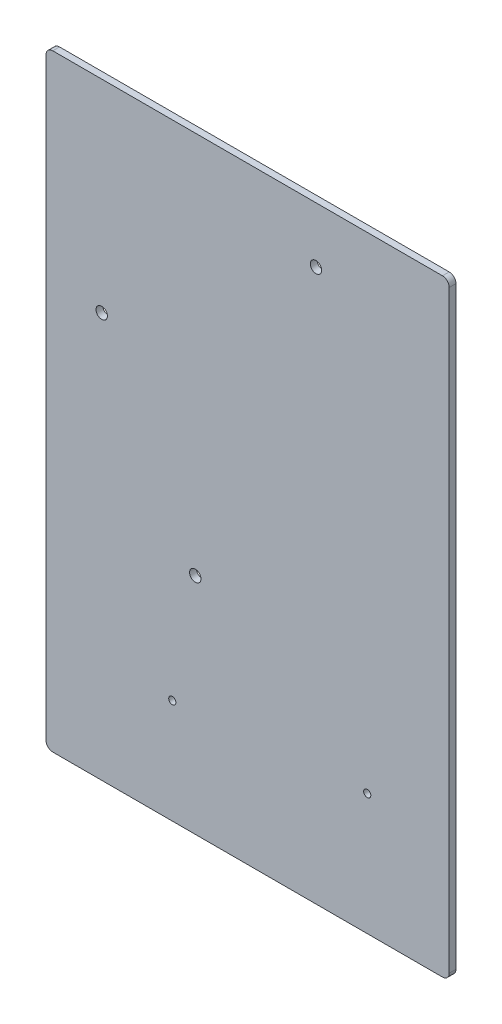
SolidWorks part; units mm, degrees
material "PC High Viscosity"
ref_plane "Front Plane" through (0, 0, 0) normal (0, 0, 1) x (1, 0, 0)
ref_plane "Top Plane" through (0, 0, 0) normal (0, 1, 0) x (1, 0, 0)
ref_plane "Right Plane" through (0, 0, 0) normal (1, 0, 0) x (0, 0, -1)
sketch "Sketch1" plane through (0, 0, 0) normal (0, 0, 1) x (1, 0, 0)
  line L0 (0, 0) -> (0, 571.5)
  line L1 (0, 0) -> (379.4125, 0)
  line L2 (381, 355.6) -> (425.45, 355.6) construction
  line L3 (381, 355.6) -> (381, 400.05) construction
  line L4 (381, 400.05) -> (425.45, 400.05) construction
  line L5 (425.45, 355.6) -> (425.45, 400.05) construction
  line L6 (379.4125, 0) -> (379.4125, 403.225)
  line L7 (379.4125, 403.225) -> (428.625, 403.225)
  line L8 (428.625, 403.225) -> (428.625, 355.6)
  line L9 (428.625, 355.6) -> (479.425, 355.6)
  line L10 (479.425, 355.6) -> (479.425, 466.725)
  line L12 (379.4125, 571.5) -> (0, 571.5)
  line L13 (379.4125, 571.5) -> (379.4125, 466.725)
  line L14 (379.4125, 466.725) -> (479.425, 466.725)
  dimension "D1" = 571.5
  dimension "D2" = 44.45
  dimension "D3" = 400.05
  dimension "D4" = 381
  dimension "D5" = 3.175
  dimension "D6" = 3.175
  dimension "D7" = 3.175
  dimension "D8" = 50.8
  dimension "D9" = 63.5
extrude "Boss-Extrude1" add sketch "Sketch1" along normal blind 6.35
fillet "Fillet1" radius 3.175 2 edges at (428.625, 403.225, 3.175) (379.4125, 403.225, 3.175)
fillet "Fillet2" radius 44.45 2 edges at (479.425, 466.725, 3.175) (379.4125, 466.725, 3.175)
hole_wizard "1/4 Clearance Hole1" positions "Sketch2" profile "Sketch3" hole size "1/4" standard "ANSI Inch" end condition through all
sketch "Sketch2" plane through (0, 0, 0) normal (0, 0, -1) x (-1, 0, 0)
  line L0 (0, 77.4886) -> (-379.4125, 110.6829) construction
  line L1 (0, 571.5) -> (0, 0) construction
  line L2 (-379.4125, 0) -> (-379.4125, 400.05) construction
  line L4 (0, 0) -> (-379.4125, 0) construction
  line L5 (-320.0116, 93.5432) -> (-104.9332, 74.7262) construction
  line L6 (-320.0116, 93.5432) -> (-316.691, 131.4982) construction
  line L7 (-104.9332, 74.7262) -> (-101.6126, 112.6813) construction
  line L8 (-316.691, 131.4982) -> (-101.6126, 112.6813) construction
  line L9 (-319.8049, 95.9065) -> (-104.7264, 77.0896) construction
  line L11 (0, 0) -> (-44.45, 0) construction
  line L12 (0, 0) -> (0, 571.5) construction
  line L13 (0, 571.5) -> (-44.45, 571.5) construction
  line L14 (-44.45, 0) -> (-44.45, 571.5) construction
  line L15 (-379.4125, 571.5) -> (0, 571.5) construction
  line L17 (-381, 0) -> (-425.45, 0) construction
  line L18 (-381, 0) -> (-381, 571.5) construction
  line L19 (-381, 571.5) -> (-425.45, 571.5) construction
  line L20 (-425.45, 0) -> (-425.45, 571.5) construction
  line L21 (-379.4125, 121.05) -> (-44.45, 91.7445) construction
  line L23 (-209.1518, 122.0897) -> (-212.4724, 84.1347) construction
  line L24 (-318.9747, 105.3953) -> (-103.8963, 86.5783) construction
  line L25 (-319.6665, 97.488) -> (-104.5881, 78.671) construction
  line L27 (-104.4497, 80.2525) -> (-319.5281, 99.0694) construction
  line L28 (-425.45, 44.45) -> (0, 44.45) construction
  point P0 (-118.8107, 98.2503)
  point P2 (-302.26, 114.3)
  point P213 (-209.1518, 122.0897)
  dimension "D2" = 5
  dimension "D3" = 2.3724
  dimension "D4" = 38.1
  dimension "D5" = 215.9
  dimension "D6" = 44.45
  dimension "D7" = 0
  dimension "D8" = 381
  dimension "D9" = 15.875
  dimension "D10" = 184.15
  dimension "D11" = 1.5875
  dimension "D12" = 1.5875
  dimension "D13" = 6.35
  dimension "D14" = 44.45
  dimension "D15" = 302.26
  dimension "D16" = 114.3
sketch "Sketch3" plane through (118.8107, 98.2503, 0) normal (1, 0, 0) x (0, 1, 0)
  line L0 (0, 0) -> (0, 6.35)
  line L1 (0, 6.35) -> (3.3782, 6.35)
  line L2 (3.3782, 6.35) -> (3.3782, 0)
  line L5 (3.3782, 0) -> (0, 0)
  line L11 (0, -6.35) -> (0, 107.95) construction
  dimension "Thru Hole Dia." = 6.7564
  dimension "Thru Hole Depth" = 6.35
sketch "Sketch4" plane through (0, 0, 0) normal (0, 0, -1) x (-1, 0, 0)
  line L1 (-379.4125, 511.175) -> (-479.425, 511.175)
  line L2 (-379.4125, 511.175) -> (-379.4125, 355.6)
  line L3 (-379.4125, 355.6) -> (-479.425, 355.6)
  line L4 (-479.425, 511.175) -> (-479.425, 355.6)
extrude "Cut-Extrude1" cut sketch "Sketch4" against normal through all
hole_wizard "27/64 (0.42188) Diameter Hole1" positions "Sketch6" profile "Sketch7" hole size "27/64" standard "ANSI Inch" end condition through all
sketch "Sketch6" plane through (0, 0, 0) normal (0, 0, -1) x (-1, 0, 0)
  line L0 (-44.45, 571.5) -> (-44.45, 0) construction
  line L1 (0, 571.5) -> (0, 0) construction
  line L2 (0, 0) -> (-379.4125, 0) construction
  line L3 (0, 381) -> (-52.3875, 381) construction
  line L4 (-254, 571.5) -> (-254, 519.1125) construction
  line L5 (-379.4125, 571.5) -> (0, 571.5) construction
  line L6 (-379.4125, 571.5) -> (0, 571.5) construction
  line L7 (0, 0) -> (-379.4125, 0) construction
  point P0 (-254, 519.1125)
  point P2 (-52.3875, 381)
  point P4 (-140.462, 210.82)
  dimension "D1" = 44.45
  dimension "D2" = 7.9375
  dimension "D3" = 210.82
  dimension "D4" = 381
  dimension "D5" = 254
  dimension "D6" = 140.462
sketch "Sketch7" plane through (254, 519.1125, 0) normal (1, 0, 0) x (0, 1, 0)
  line L0 (0, 0) -> (0, 6.35)
  line L1 (0, 6.35) -> (5.3579, 6.35)
  line L2 (5.3579, 6.35) -> (5.3579, 0)
  line L5 (5.3579, 0) -> (0, 0)
  line L11 (0, -6.35) -> (0, 107.95) construction
  dimension "Thru Hole Dia." = 10.7158
  dimension "Thru Hole Depth" = 6.35
fillet "Fillet3" radius 6.35 4 edges at (379.4125, 0, 3.175) (0, 571.5, 3.175) (379.4125, 571.5, 3.175) (0, 0, 3.175)
